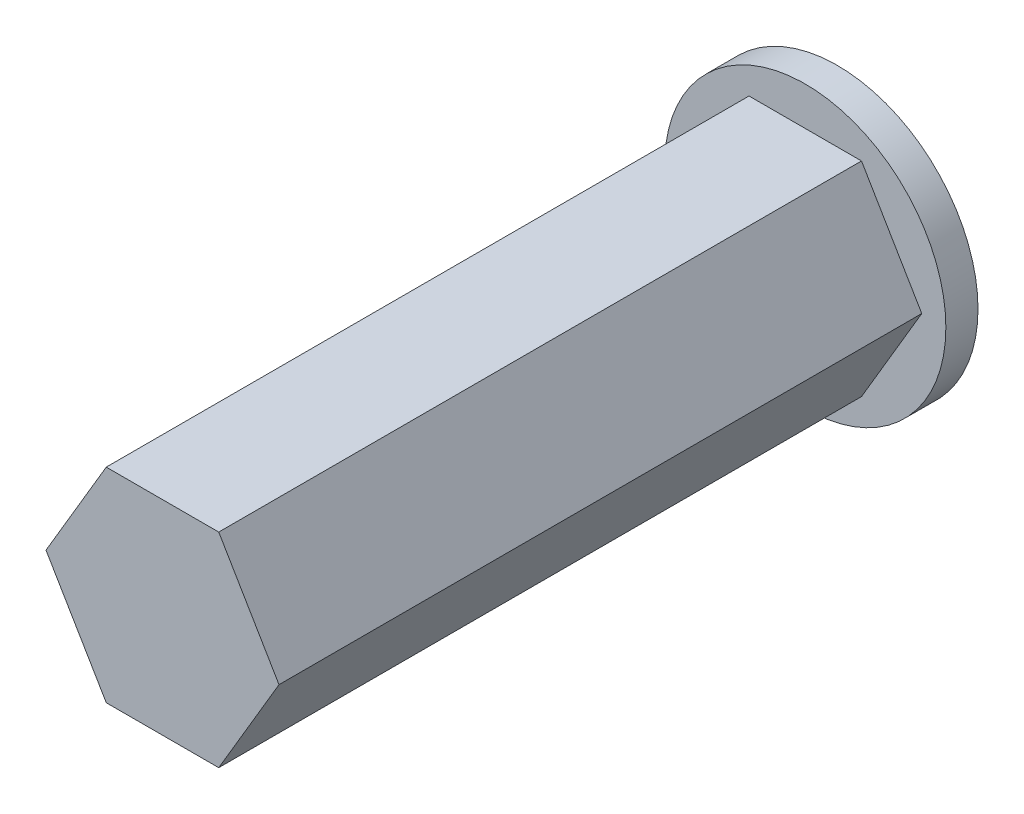
SolidWorks part; units mm, degrees
ref_plane "Front Plane" through (0, 0, 0) normal (0, 0, 1) x (1, 0, 0)
ref_plane "Top Plane" through (0, 0, 0) normal (0, 1, 0) x (1, 0, 0)
ref_plane "Right Plane" through (0, 0, 0) normal (1, 0, 0) x (0, 0, -1)
sketch "Sketch1" plane through (0, 0, 0) normal (0, 0, 1) x (1, 0, 0)
  circle A0 centre (0, 0) radius 8.75
  dimension "D1" = 17.5
extrude "Boss-Extrude1" add sketch "Sketch1" along normal blind 2
sketch "Sketch2" plane through (0, 0, 2) normal (0, 0, 1) x (1, 0, 0)
  line L0 (0, 0) -> (0, 6.35) construction
  line L1 (7.25, 0) -> (-7.25, 0) construction
  line L2 (3.5, 6.35) -> (-3.5, 6.35)
  line L3 (-3.5, 6.35) -> (-7.25, 0)
  line L4 (3.5, 6.35) -> (7.25, 0)
  line L5 (3.5, -6.35) -> (7.25, 0)
  line L6 (-3.5, -6.35) -> (-7.25, 0)
  line L7 (3.5, -6.35) -> (-3.5, -6.35)
  dimension "D1" = 6.35
  dimension "D2" = 7.25
  dimension "D3" = 3.5
extrude "Boss-Extrude2" add sketch "Sketch2" along normal blind 40
